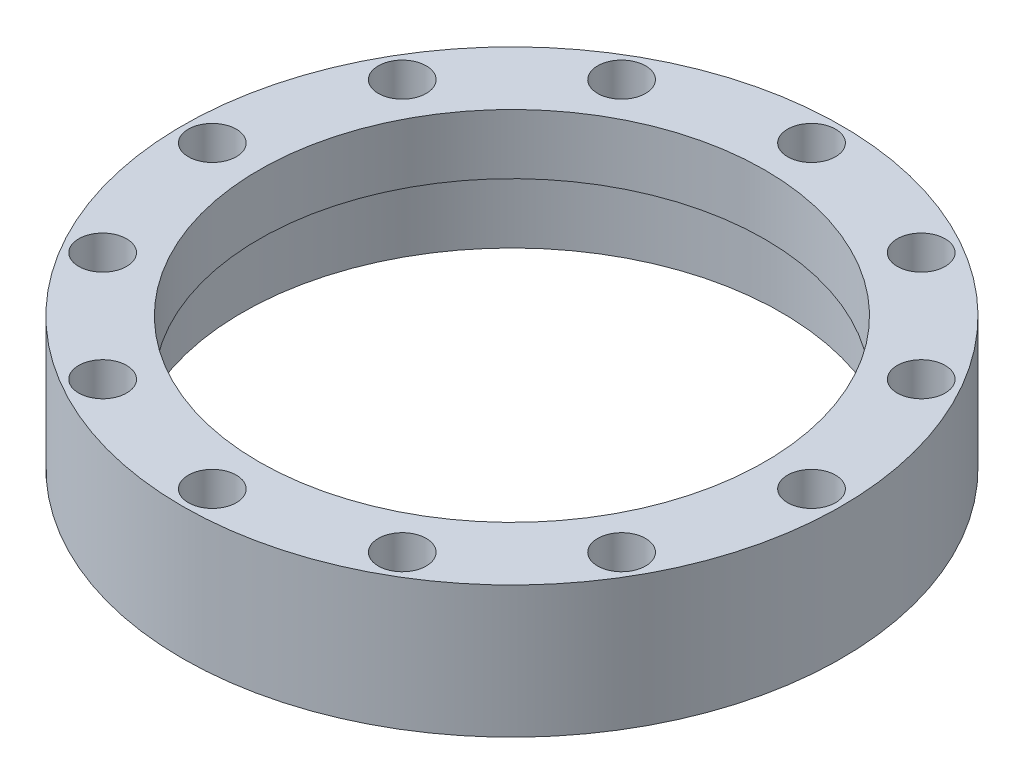
SolidWorks part; units mm, degrees
ref_plane "Front Plane" through (0, 0, 0) normal (0, 0, 1) x (1, 0, 0)
ref_plane "Top Plane" through (0, 0, 0) normal (0, 1, 0) x (1, 0, 0)
ref_plane "Right Plane" through (0, 0, 0) normal (1, 0, 0) x (0, 0, -1)
sketch "Sketch1" plane through (0, 0, 0) normal (0, 1, 0) x (1, 0, 0)
  line L0 (0, 48.2621) -> (0, -49.945) construction
  circle A0 centre (0, 0) radius 27.5
  circle A1 centre (0, 0) radius 25 construction
  circle A2 centre (0, 0) radius 22.5
  circle A3 centre (0, 25) radius 1.6
  circle A4 centre (12.5, 21.6506) radius 1.6
  circle A5 centre (21.6506, 12.5) radius 1.6
  circle A6 centre (25, 0) radius 1.6
  circle A7 centre (21.6506, -12.5) radius 1.6
  circle A8 centre (12.5, -21.6506) radius 1.6
  circle A9 centre (0, -25) radius 1.6
  circle A10 centre (-12.5, -21.6506) radius 1.6
  circle A11 centre (-21.6506, -12.5) radius 1.6
  circle A12 centre (-25, 0) radius 1.6
  circle A13 centre (-21.6506, 12.5) radius 1.6
  circle A14 centre (-12.5, 21.6506) radius 1.6
  point P31 (0, 0)
  dimension "D1" = 55
  dimension "D2" = 50
  dimension "D3" = 45
  dimension "D4" = 3.2
  dimension "D5" = 12
extrude "Boss-Extrude1" add sketch "Sketch1" along normal blind 11
sketch "Sketch2" plane through (0, 11, 0) normal (0, 1, 0) x (1, 0, 0)
  circle A0 centre (0, 0) radius 22.5
  circle A1 centre (0, 0) radius 21.1
  dimension "D1" = 42.2
extrude "Boss-Extrude2" add sketch "Sketch2" against normal blind 5
sketch "Sketch3" plane through (0, 11, 0) normal (0, 1, 0) x (1, 0, 0)
  circle A0 centre (0, 25) radius 2
  circle A1 centre (12.5, 21.6506) radius 2
  circle A2 centre (21.6506, 12.5) radius 2
  circle A3 centre (25, 0) radius 2
  circle A4 centre (21.6506, -12.5) radius 2
  circle A5 centre (12.5, -21.6506) radius 2
  circle A6 centre (0, -25) radius 2
  circle A7 centre (-12.5, -21.6506) radius 2
  circle A8 centre (-21.6506, -12.5) radius 2
  circle A9 centre (-25, 0) radius 2
  circle A10 centre (-21.6506, 12.5) radius 2
  circle A11 centre (-12.5, 21.6506) radius 2
  point P28 (0, 0)
  dimension "D1" = 4
  dimension "D2" = 12
extrude "Cut-Extrude1" cut sketch "Sketch3" against normal blind 5
